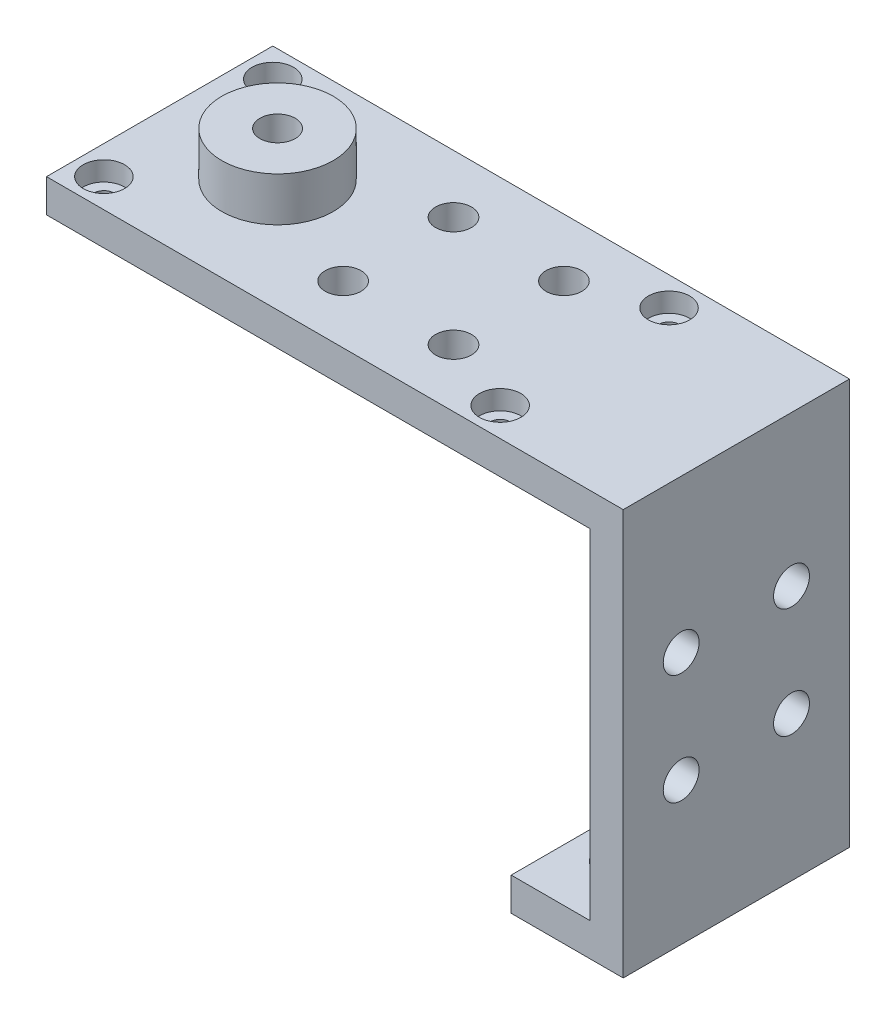
SolidWorks part; units mm, degrees
ref_plane "Front Plane" through (0, 0, 0) normal (0, 0, 1) x (1, 0, 0)
ref_plane "Top Plane" through (0, 0, 0) normal (0, 1, 0) x (1, 0, 0)
ref_plane "Right Plane" through (0, 0, 0) normal (1, 0, 0) x (0, 0, -1)
sketch "Sketch1" plane through (0, 0, 0) normal (0, 1, 0) x (1, 0, 0)
  line L1 (-26.125, -10.25) -> (26.125, -10.25)
  line L2 (-26.125, -10.25) -> (-26.125, 10.25)
  line L3 (-26.125, 10.25) -> (26.125, 10.25)
  line L4 (26.125, -10.25) -> (26.125, 10.25)
  line L5 (-26.125, -10.25) -> (26.125, 10.25) construction
  line L6 (-26.125, 10.25) -> (26.125, -10.25) construction
  point P0 (0, 0)
  dimension "D1" = 52.25
  dimension "D2" = 20.5
extrude "Boss-Extrude1" add sketch "Sketch1" against normal blind 3
sketch "Sketch2" plane through (0, -3, 0) normal (0, -1, 0) x (1, 0, 0)
  line L0 (26.125, -10.25) -> (-26.125, -10.25) construction
  line L1 (26.125, 10.25) -> (23.125, 10.25)
  line L2 (26.125, 10.25) -> (26.125, -10.25)
  line L3 (26.125, -10.25) -> (23.125, -10.25)
  line L4 (23.125, 10.25) -> (23.125, -10.25)
  dimension "D1" = 3
extrude "Boss-Extrude2" add sketch "Sketch2" along normal blind 33.75
sketch "Sketch3" plane through (23.125, 0, 0) normal (-1, 0, 0) x (0, 0, 1)
  line L0 (10.25, -36.75) -> (10.25, -3) construction
  line L1 (-10.25, -36.75) -> (10.25, -36.75)
  line L2 (-10.25, -36.75) -> (-10.25, -33.75)
  line L3 (-10.25, -33.75) -> (10.25, -33.75)
  line L4 (10.25, -36.75) -> (10.25, -33.75)
  dimension "D1" = 3
extrude "Boss-Extrude3" add sketch "Sketch3" along normal blind 7.15
sketch "Sketch4" plane through (0, -36.75, 0) normal (0, -1, 0) x (1, 0, 0)
  line L1 (15.975, -10.25) -> (26.125, -10.25) construction
  line L2 (15.975, -10.25) -> (15.975, 10.25) construction
  line L4 (26.125, 10.25) -> (15.975, 10.25) construction
  circle A0 centre (19.575, 4.475) radius 1.625
  circle A1 centre (19.575, -4.475) radius 1.625
  dimension "D1" = 3.25
  dimension "D2" = 3.25
  dimension "D3" = 5.775
  dimension "D4" = 5.775
  dimension "D5" = 3.6
  dimension "D6" = 3.6
extrude "Cut-Extrude1" cut sketch "Sketch4" against normal up to surface (3 mm away) up to face at (19.55, -33.75, 0)
sketch "Sketch5" plane through (15.975, 0, 0) normal (-1, 0, 0) x (0, 0, 1)
  line L0 (10.25, -33.75) -> (-10.25, -33.75) construction
  line L1 (-0.6647, -35.05) -> (1.1353, -35.05)
  line L2 (-0.6647, -35.05) -> (-0.6647, -33.75)
  line L3 (-0.6647, -33.75) -> (1.1353, -33.75)
  line L4 (1.1353, -35.05) -> (1.1353, -33.75)
  line L5 (-0.6647, -35.05) -> (1.1353, -33.75) construction
  line L6 (-0.6647, -33.75) -> (1.1353, -35.05) construction
  point P0 (0.2353, -34.4)
  dimension "D1" = 1.3
  dimension "D2" = 1.8
extrude "Cut-Extrude2" cut sketch "Sketch5" against normal up to surface (7.15 mm away) up to face at (23.125, -18.375, 0)
sketch "Sketch6" plane through (23.125, 0, 0) normal (-1, 0, 0) x (0, 0, 1)
  line L0 (10.25, -33.75) -> (10.25, -3) construction
  line L2 (-0.6647, -33.75) -> (-10.25, -33.75) construction
  circle A0 centre (-4.9978, -13.625) radius 1.625
  circle A1 centre (-4.9978, -23.625) radius 1.625
  circle A2 centre (5, -23.8361) radius 1.625
  circle A3 centre (5, -13.8361) radius 1.625
  dimension "D1" = 3.25
  dimension "D2" = 3.25
  dimension "D3" = 3.25
  dimension "D4" = 3.25
  dimension "D5" = 10
  dimension "D6" = 10
  dimension "D7" = 10
  dimension "D8" = 10
  dimension "D9" = 5.25
  dimension "D10" = 10.125
extrude "Cut-Extrude3" cut sketch "Sketch6" against normal up to surface (3 mm away) up to face at (26.125, -18.375, 0)
sketch "Sketch7" plane through (0, 0, 0) normal (0, 1, 0) x (1, 0, 0)
  line L0 (26.125, 10.25) -> (-26.125, 10.25) construction
  line L5 (26.125, -10.25) -> (26.125, 10.25) construction
  circle A0 centre (-4.5, 5) radius 1.625
  circle A1 centre (-4.5, -5) radius 1.625
  circle A2 centre (5.5, 5) radius 1.625
  circle A3 centre (5.5, -5) radius 1.625
  dimension "D1" = 3.25
  dimension "D2" = 3.25
  dimension "D3" = 3.25
  dimension "D4" = 3.25
  dimension "D5" = 10
  dimension "D6" = 10
  dimension "D7" = 10
  dimension "D8" = 10
  dimension "D9" = 5.25
  dimension "D10" = 20.625
  dimension "D11" = 0
extrude "Cut-Extrude4" cut sketch "Sketch7" against normal up to surface (3 mm away) up to face at (-1.5, -3, 0)
sketch "Sketch8" plane through (0, 0, 0) normal (0, 1, 0) x (1, 0, 0)
  line L0 (26.125, 10.25) -> (-26.125, 10.25) construction
  line L2 (-26.125, 10.25) -> (-26.125, -10.25) construction
  circle A0 centre (-23.525, 7.65) radius 1.875
  circle A1 centre (-23.525, -7.65) radius 1.875
  circle A2 centre (12.375, 7.65) radius 1.875
  circle A3 centre (12.375, -7.65) radius 1.875
  dimension "D1" = 3.75
  dimension "D2" = 3.75
  dimension "D3" = 3.75
  dimension "D4" = 3.75
  dimension "D5" = 15.3
  dimension "D6" = 15.3
  dimension "D7" = 35.9
  dimension "D8" = 35.9
  dimension "D9" = 2.6
  dimension "D10" = 2.6
  dimension "D11" = 2.6
extrude "Cut-Extrude5" cut sketch "Sketch8" against normal blind 1.75
sketch "Sketch9" plane through (0, -1.75, 0) normal (0, 1, 0) x (1, 0, 0)
  circle A0 centre (-23.525, 7.65) radius 0.925
  circle A1 centre (-23.525, -7.65) radius 0.925
  circle A2 centre (12.375, -7.65) radius 0.925
  circle A3 centre (12.375, 7.65) radius 0.925
  dimension "D1" = 1.85
  dimension "D2" = 1.85
  dimension "D3" = 1.85
  dimension "D4" = 1.85
extrude "Cut-Extrude6" cut sketch "Sketch9" against normal up to surface (1.25 mm away) up to face at (-4.5, -3, 3.375)
sketch "Sketch11" plane through (0, -3, 0) normal (0, -1, 0) x (1, 0, 0)
  circle A0 centre (-15.4428, 0) radius 4
  dimension "D1" = 8
sketch "Sketch12" plane through (0, 0, 0) normal (0, 1, 0) x (1, 0, 0)
  circle A0 centre (-15.4428, 0) radius 5.05
  dimension "D1" = 10.1
extrude "Boss-Extrude4" add sketch "Sketch12" along normal blind 4
extrude "Cut-Extrude7" cut sketch "Sketch11" against normal blind 3
sketch "Sketch13" plane through (0, 0, 0) normal (0, -1, 0) x (1, 0, 0)
  circle A0 centre (-15.4428, 0) radius 1.6
  dimension "D1" = 3.2
extrude "Cut-Extrude8" cut sketch "Sketch13" against normal up to surface (4 mm away) up to face at (-15.4428, 4, 5.05)
sketch "Sketch14" plane through (0, 0, 0) normal (0, 1, 0) x (1, 0, 0)
